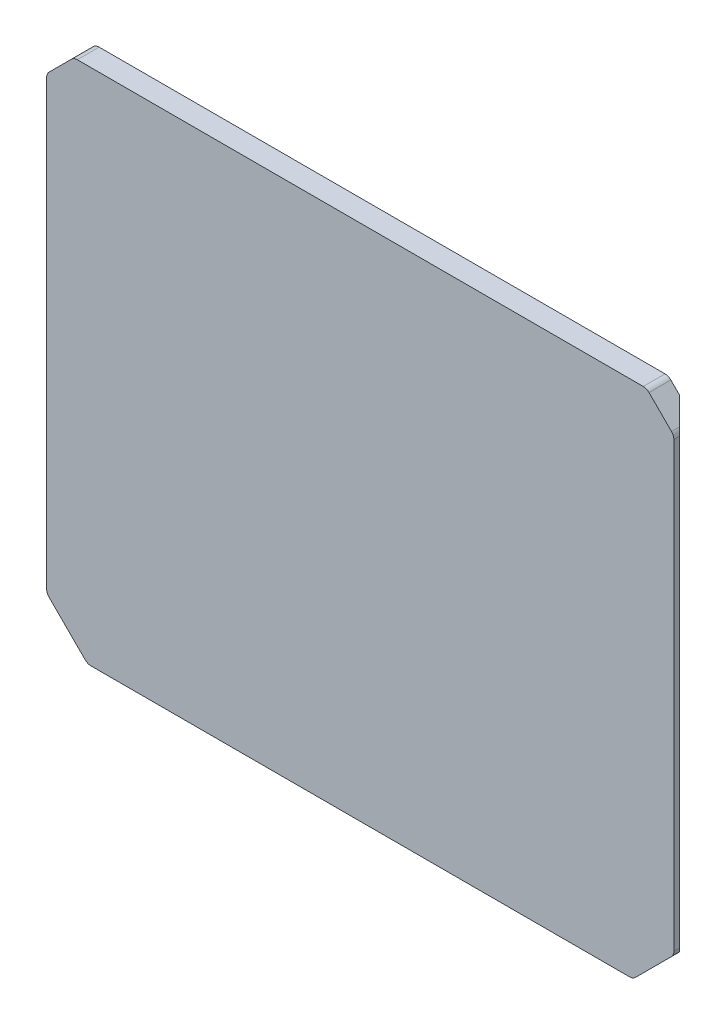
SolidWorks part; units mm, degrees
ref_plane "Plane1" through (0, 0, 0) normal (0, 0, 1) x (1, 0, 0)
ref_plane "Plane2" through (0, 0, 0) normal (0, 1, 0) x (1, 0, 0)
ref_plane "Plane3" through (0, 0, 0) normal (1, 0, 0) x (0, 0, -1)
sketch "Sketch1" plane through (0, 0, 0) normal (0, 0, 1) x (1, 0, 0)
  line L0 (100, 0) -> (115, 15)
  line L1 (-100, 0) -> (100, 0)
  line L2 (-115, 15) -> (-115, 180)
  line L3 (-105, 190) -> (105, 190)
  line L4 (115, 15) -> (115, 180)
  line L5 (-115, 15) -> (-100, 0)
  line L6 (-115, 180) -> (-105, 190)
  line L7 (105, 190) -> (115, 180)
  point P0 (-115, 0)
  point P1 (115, 190)
  point P2 (-115, 190)
  point P3 (115, 0)
  dimension "D1" = 230
  dimension "D2" = 190
extrude "Base-Extrude" add sketch "Sketch1" along normal blind 8
chamfer "Skærpning1 sider" distance 6 angle 45 2 edges at (-115, 97.5, 0) (115, 97.5, 0)
fillet "R3 rundinger" radius 3 8 edges at (-100, 0, 4) (-115, 15, 7) (-115, 180, 7) (-105, 190, 4) (105, 190, 4) (115, 180, 7) (115, 15, 7) (100, 0, 4)
